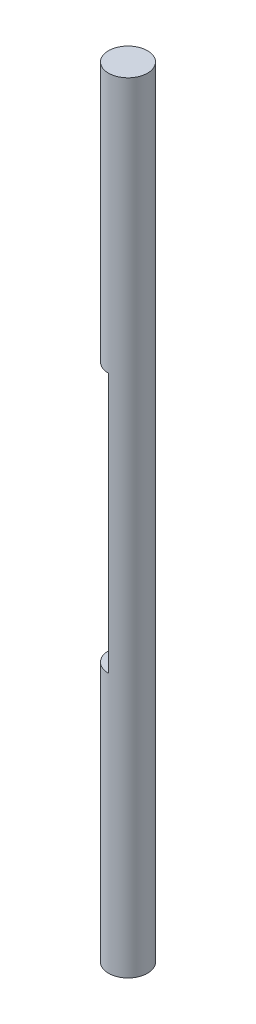
SolidWorks part; units mm, degrees
ref_plane "前视基准面" through (0, 0, 0) normal (0, 0, 1) x (1, 0, 0)
ref_plane "上视基准面" through (0, 0, 0) normal (0, 1, 0) x (1, 0, 0)
ref_plane "右视基准面" through (0, 0, 0) normal (1, 0, 0) x (0, 0, -1)
sketch "草图1" plane through (0, 0, 0) normal (0, 1, 0) x (1, 0, 0)
  circle A0 centre (0, 0) radius 1.5
extrude "凸台-拉伸1" add sketch "草图1" along normal blind 60
sketch "草图2" plane through (0, 0, 0) normal (1, 0, 0) x (0, 0, -1)
  line L0 (0, 0) -> (0, 60)
  line L1 (1.5, 60) -> (-1.5, 60) construction
  line L3 (-3.0948, 40) -> (3.0948, 40)
  line L4 (-3.0948, 40) -> (-3.0948, 20)
  line L5 (-3.0948, 20) -> (3.0948, 20)
  line L6 (3.0948, 40) -> (3.0948, 20)
  line L7 (-3.0948, 40) -> (3.0948, 20) construction
  line L8 (-3.0948, 20) -> (3.0948, 40) construction
  point P5 (0, 30)
  dimension "D1" = 20
extrude "切除-拉伸1" cut sketch "草图2" against normal blind 40 contours L6 L3 L0 L5 | L4 L5 L0 L3
